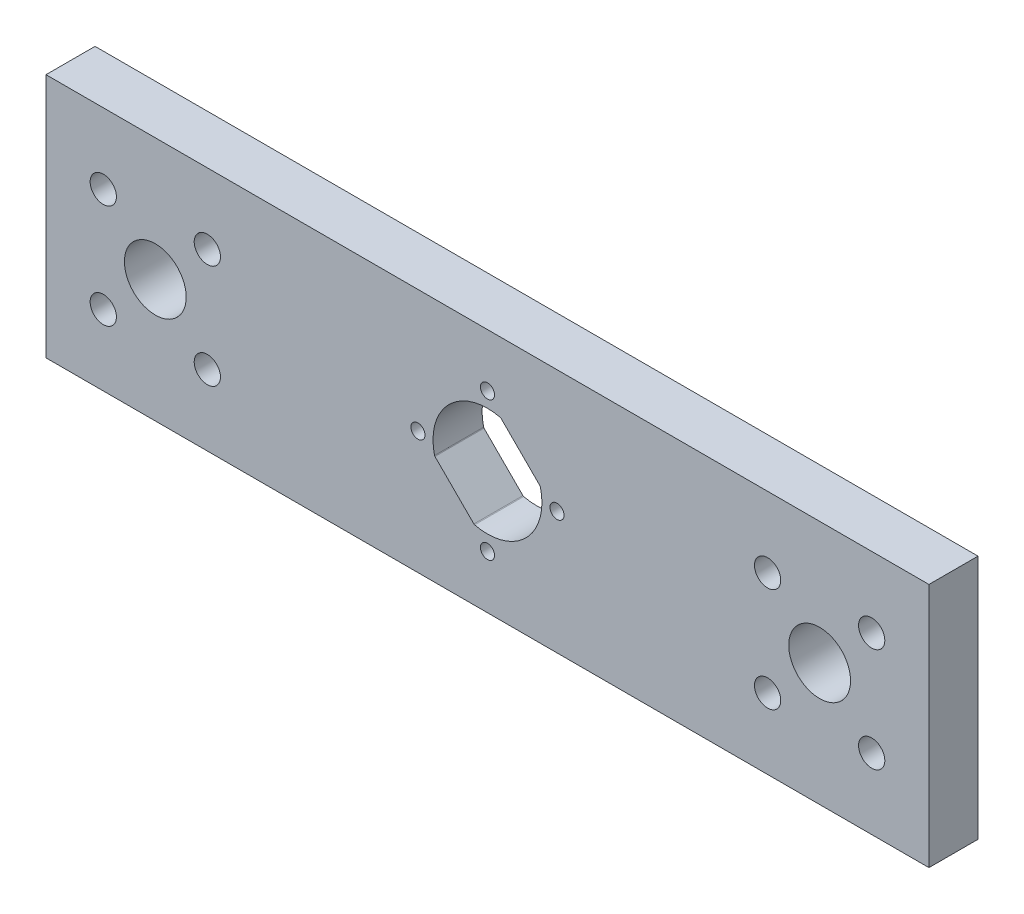
SolidWorks part; units mm, degrees
ref_plane "Front Plane" through (0, 0, 0) normal (0, 0, 1) x (1, 0, 0)
ref_plane "Top Plane" through (0, 0, 0) normal (0, 1, 0) x (1, 0, 0)
ref_plane "Right Plane" through (0, 0, 0) normal (1, 0, 0) x (0, 0, -1)
sketch "Sketch1" plane through (0, 0, 0) normal (0, 0, 1) x (1, 0, 0)
  line L0 (-6.7979, -1.7581) -> (-1.7581, -6.7979)
  line L1 (-57.15, 15.875) -> (57.15, 15.875)
  line L2 (-57.15, 15.875) -> (-57.15, -15.875)
  line L3 (-57.15, -15.875) -> (57.15, -15.875)
  line L4 (57.15, 15.875) -> (57.15, -15.875)
  line L5 (-57.15, 15.875) -> (57.15, -15.875) construction
  line L6 (-57.15, -15.875) -> (57.15, 15.875) construction
  line L7 (6.7979, 1.7581) -> (1.7581, 6.7979)
  line L16 (0, 9) -> (0, -9) construction
  line L17 (-9, 0) -> (9, 0) construction
  line L18 (-57.15, 0) -> (57.15, 0) construction
  line L19 (0, 15.875) -> (0, -15.875) construction
  line L20 (-43, 0) -> (-36.2648, 6.7352) construction
  line L21 (-43, -4) -> (-43, 4) construction
  line L22 (-43, 0) -> (-49.7352, 6.7352) construction
  line L23 (-43, 0) -> (-36.2648, -6.7352) construction
  line L24 (-43, 0) -> (-49.7352, -6.7352) construction
  line L25 (43, 0) -> (49.7352, -6.7352) construction
  line L26 (43, -4) -> (43, 4) construction
  line L27 (43, 0) -> (36.2648, -6.7352) construction
  line L28 (43, 0) -> (36.2648, 6.7352) construction
  line L29 (43, 0) -> (49.7352, 6.7352) construction
  circle A8 centre (-9, 0) radius 0.9115
  circle A9 centre (0, -9) radius 0.9115
  arc A10 (1.7581, 6.7979) -> (1.6639, 6.8508) centre (1.6167, 6.6565) ccw
  arc A11 (-6.8508, -1.6639) -> (-6.7979, -1.7581) centre (-6.6565, -1.6167) ccw
  arc A12 (1.6639, 6.8508) -> (-6.8508, -1.6639) centre (0, 0) ccw
  arc A13 (-1.7581, -6.7979) -> (-1.6639, -6.8508) centre (-1.6167, -6.6565) ccw
  arc A14 (-1.6639, -6.8508) -> (6.8508, 1.6639) centre (0, 0) ccw
  arc A15 (6.8508, 1.6639) -> (6.7979, 1.7581) centre (6.6565, 1.6167) ccw
  circle A16 centre (9, 0) radius 0.9115
  circle A17 centre (0, 9) radius 0.9115
  circle A22 centre (-43, 0) radius 4
  circle A23 centre (43, 0) radius 4
  circle A24 centre (-36.2648, 6.7352) radius 1.7
  circle A25 centre (-49.7352, 6.7352) radius 1.7
  circle A26 centre (-36.2648, -6.7352) radius 1.7
  circle A27 centre (-49.7352, -6.7352) radius 1.7
  circle A28 centre (49.7352, -6.7352) radius 1.7
  circle A29 centre (36.2648, -6.7352) radius 1.7
  circle A30 centre (36.2648, 6.7352) radius 1.7
  circle A31 centre (49.7352, 6.7352) radius 1.7
  point P0 (0, 0)
  dimension "D5" = 1.823
  dimension "D6" = 1.823
  dimension "D7" = 1.823
  dimension "D8" = 1.823
  dimension "D9" = 8
  dimension "D10" = 8
  dimension "D13" = 3.4
  dimension "D1" = 114.3
  dimension "D2" = 31.75
  dimension "D3" = 18
  dimension "D4" = 18
  dimension "D11" = 43
  dimension "D12" = 43
  dimension "D14" = 45
  dimension "D15" = 9.525
  dimension "D16" = 9.525
extrude "Boss-Extrude1" add sketch "Sketch1" along normal blind 6.35
equation "\"MOTOR_CENTER_DIST\"= 43mm"
equation "\"D11@Sketch1\"=\"MOTOR_CENTER_DIST\""
equation "\"D12@Sketch1\"=\"MOTOR_CENTER_DIST\""
